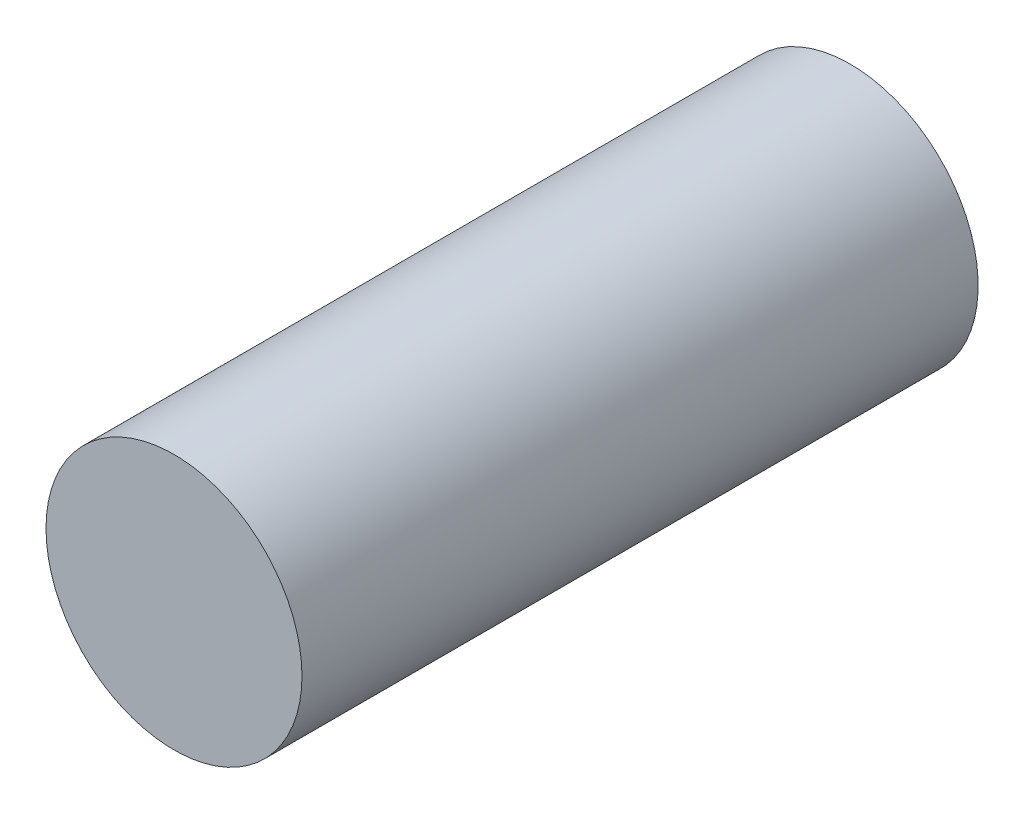
SolidWorks part; units mm, degrees
ref_plane "Front Plane" through (0, 0, 0) normal (0, 0, 1) x (1, 0, 0)
ref_plane "Top Plane" through (0, 0, 0) normal (0, 1, 0) x (1, 0, 0)
ref_plane "Right Plane" through (0, 0, 0) normal (1, 0, 0) x (0, 0, -1)
sketch "Sketch1" plane through (0, 0, 0) normal (0, 0, 1) x (1, 0, 0)
  circle A0 centre (0, 0) radius 50.8
  dimension "D1" = 101.6
extrude "Boss-Extrude1" add sketch "Sketch1" along normal blind 304.8
sketch "Sketch2" plane through (0, 0, 0) normal (0, 0, -1) x (-1, 0, 0)
  line L0 (0, -62.5) -> (0, 62.5) construction
  line L1 (0, 62.5) -> (0, -62.5)
  arc A0 (0, -62.5) -> (0, 62.5) centre (0, 0) ccw
  dimension "D1" = 125
revolve "Cut-Revolve3" cut sketch "Sketch2" angle 180 about L0
